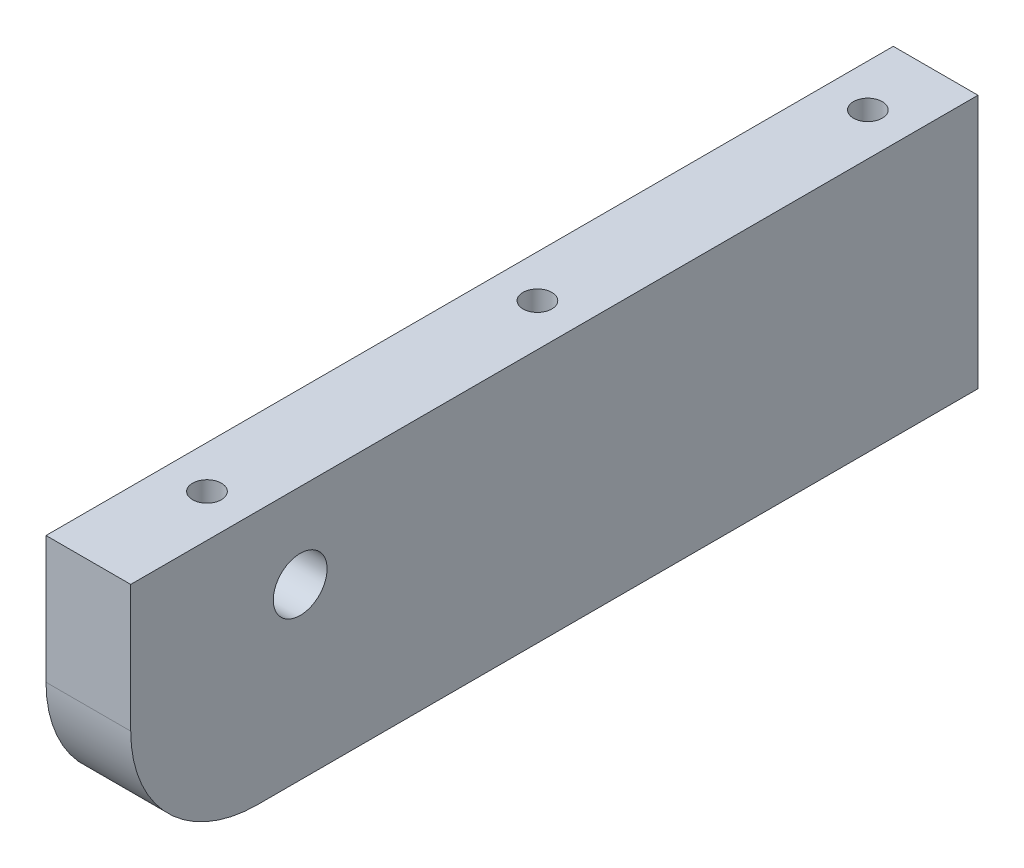
SolidWorks part; units mm, degrees
ref_plane "Front Plane" through (0, 0, 0) normal (0, 0, 1) x (1, 0, 0)
ref_plane "Top Plane" through (0, 0, 0) normal (0, 1, 0) x (1, 0, 0)
ref_plane "Right Plane" through (0, 0, 0) normal (1, 0, 0) x (0, 0, -1)
sketch "Sketch1" plane through (0, 0, 0) normal (1, 0, 0) x (0, 0, -1)
  line L1 (-50, -15) -> (50, -15)
  line L2 (-50, -15) -> (-50, 15)
  line L3 (-50, 15) -> (50, 15)
  line L4 (50, -15) -> (50, 15)
  line L5 (-50, -15) -> (50, 15) construction
  line L6 (-50, 15) -> (50, -15) construction
  circle A0 centre (-30, 5) radius 3.175
  point P0 (0, 0)
  dimension "D3" = 6.35
  dimension "D1" = 30
  dimension "D2" = 100
  dimension "D4" = 20
  dimension "D5" = 10
extrude "Boss-Extrude1" add sketch "Sketch1" along normal blind 10
fillet "Fillet1" radius 15 1 edges at (5, -15, 50)
hole_wizard "CBORE for M3 SHCS" positions "Sketch4" profile "Sketch5" counterbore size "M3" standard "ANSI Metric"
sketch "Sketch4" plane through (-726.2935, 25, -1323.2827) normal (0, 1, 0) x (1, 0, 0)
  line L3 (621.2935, -1281.2827) -> (621.2935, -1365.2827) construction
  line L5 (731.2935, -1281.2827) -> (731.2935, -1359.2827) construction
  circle A0 centre (731.2935, -1281.2827) radius 2.243
  circle A1 centre (731.2935, -1359.2827) radius 2.2384
  circle A3 centre (621.2935, -1281.2827) radius 2.3325
  circle A4 centre (621.2935, -1365.2827) radius 1.7576
  circle A5 centre (621.2935, -1323.2827) radius 1.8624
  circle A6 centre (731.2935, -1320.2827) radius 2.0271
  point P1 (731.2935, -1281.2827)
  point P8 (731.2935, -1359.2827)
  point P15 (621.2935, -1281.2827)
  point P17 (621.2935, -1365.2827)
  point P19 (621.2935, -1323.2827)
  point P27 (731.2935, -1320.2827)
sketch "Sketch5" plane through (5, 25, -42) normal (1, 0, 0) x (0, 0, 1)
  line L0 (0, 0) -> (0, 24.0215)
  line L1 (0, 24.0215) -> (1.7, 23)
  line L2 (1.7, 23) -> (1.7, 3)
  line L3 (1.7, 3) -> (3.25, 3)
  line L4 (3.25, 3) -> (3.25, 0)
  line L5 (3.25, 0) -> (0, 0)
  line L6 (0, 24.0215) -> (-1.7, 23) construction
  line L7 (0, -6.35) -> (0, 107.95) construction
  dimension "Hole Dia." = 3.4
  dimension "Hole Depth" = 23
  dimension "C'Bore Dia." = 6.5
  dimension "C'Bore Depth" = 3
  dimension "Drill Angle" = 118
